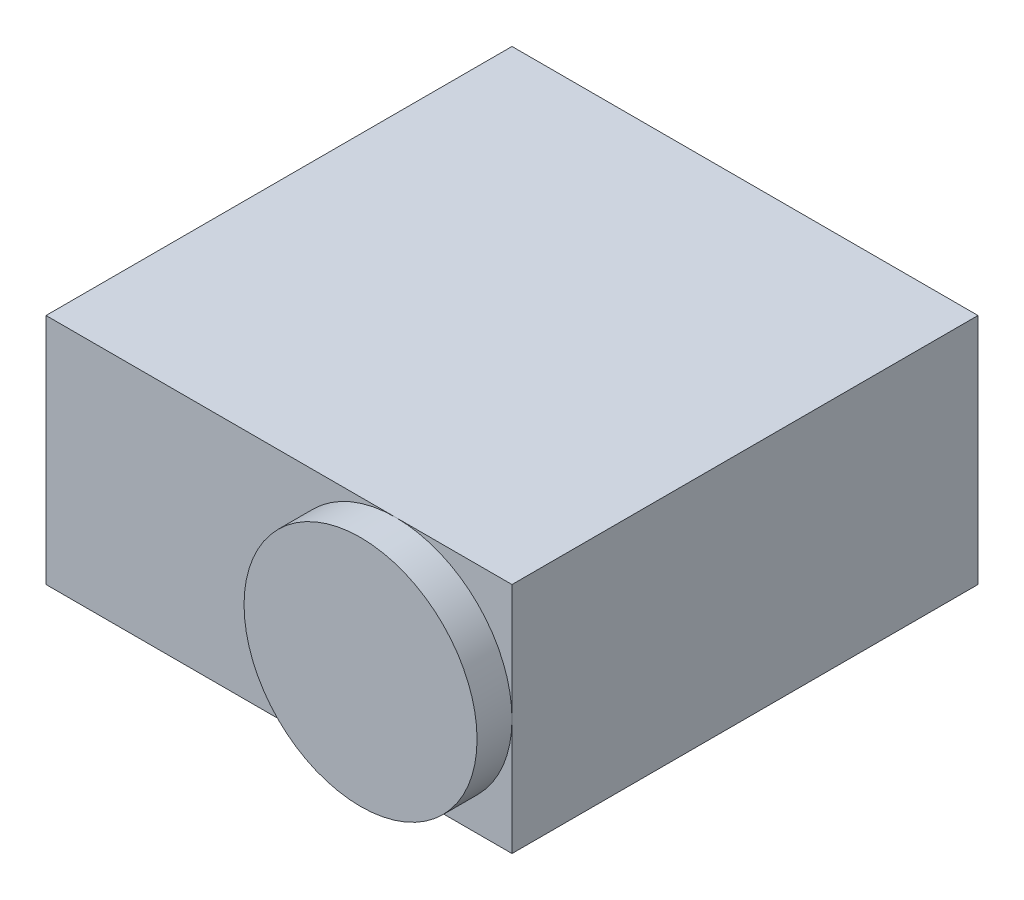
SolidWorks part; units mm, degrees
ref_plane "Front Plane" through (0, 0, 0) normal (0, 0, 1) x (1, 0, 0)
ref_plane "Top Plane" through (0, 0, 0) normal (0, 1, 0) x (1, 0, 0)
ref_plane "Right Plane" through (0, 0, 0) normal (1, 0, 0) x (0, 0, -1)
sketch "Sketch1" plane through (0, 0, 0) normal (0, 1, 0) x (1, 0, 0)
  line L1 (0, 0) -> (40, 0)
  line L2 (0, 0) -> (0, 40)
  line L3 (0, 40) -> (40, 40)
  line L4 (40, 0) -> (40, 40)
  dimension "D1" = 40
  dimension "D2" = 40
extrude "Boss-Extrude1" add sketch "Sketch1" along normal blind 20
sketch "Sketch3" plane through (0, 0, 0) normal (0, 0, 1) x (1, 0, 0)
  line L0 (0, 20) -> (40, 20) construction
  line L2 (40, 20) -> (40, 0) construction
  circle A0 centre (30, 10) radius 10
  dimension "D1" = 20
  dimension "D2" = 10
  dimension "D3" = 10
extrude "Boss-Extrude2" add sketch "Sketch3" along normal blind 3
